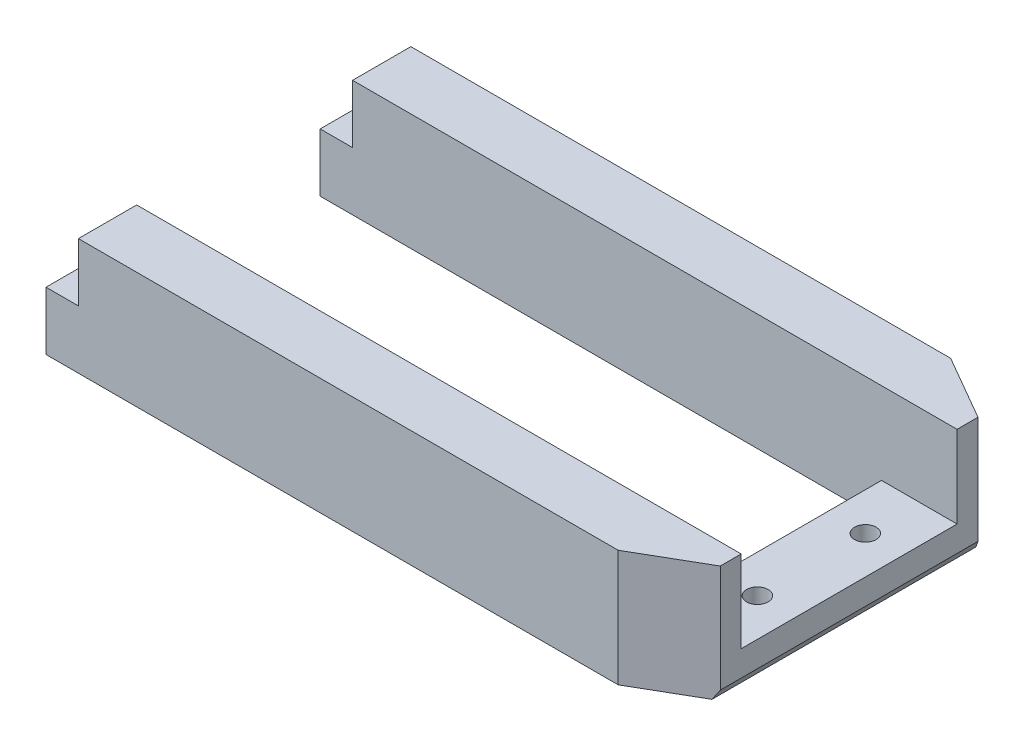
SolidWorks part; units mm, degrees
ref_plane "Alzado" through (0, 0, 0) normal (0, 0, 1) x (1, 0, 0)
ref_plane "Planta" through (0, 0, 0) normal (0, 1, 0) x (1, 0, 0)
ref_plane "Vista lateral" through (0, 0, 0) normal (1, 0, 0) x (0, 0, -1)
sketch "Croquis1" plane through (0, 0, 0) normal (0, 1, 0) x (1, 0, 0)
  line L0 (-29.0045, -14.5329) -> (-29.0045, -9.1329)
  line L1 (-29.0045, -9.1329) -> (22.9955, -9.1329)
  line L2 (22.9955, -9.1329) -> (22.9955, 10.8671)
  line L3 (22.9955, 10.8671) -> (-29.0045, 10.8671)
  line L4 (-29.0045, 10.8671) -> (-29.0045, 16.2671)
  line L5 (-29.0045, 16.2671) -> (23.9988, 16.2671)
  line L6 (23.9988, 16.2671) -> (29.9955, 12.8049)
  line L7 (29.9955, 12.8049) -> (29.9955, -11.0708)
  line L8 (29.9955, -11.0708) -> (23.9988, -14.5329)
  line L9 (23.9988, -14.5329) -> (-29.0045, -14.5329)
extrude "Saliente-Extruir1" add sketch "Croquis1" along normal blind 13
sketch "Croquis2" plane through (0, 13, 0) normal (0, 1, 0) x (1, 0, 0)
  line L0 (29.9955, -11.0708) -> (29.9955, 12.8049) construction
  line L1 (22.9955, 10.8671) -> (29.9955, 10.8671)
  line L2 (22.9955, 10.8671) -> (22.9955, -9.1329)
  line L3 (22.9955, -9.1329) -> (29.9955, -9.1329)
  line L4 (29.9955, 10.8671) -> (29.9955, -9.1329)
  dimension "D1" = 20
extrude "Cortar-Extruir1" cut sketch "Croquis2" against normal blind 7.6
sketch "Croquis3" plane through (0, 13, 0) normal (0, 1, 0) x (1, 0, 0)
  line L0 (-29.0045, 10.8671) -> (29.9955, 10.8671) construction
  line L1 (-29.0045, 16.2671) -> (-26.0045, 16.2671)
  line L2 (-29.0045, 16.2671) -> (-29.0045, 10.8671)
  line L3 (-29.0045, 10.8671) -> (-26.0045, 10.8671)
  line L4 (-26.0045, 16.2671) -> (-26.0045, 10.8671)
  line L5 (-29.0045, -14.5329) -> (23.9988, -14.5329) construction
  line L6 (-29.0045, -9.1329) -> (-26.0045, -9.1329)
  line L7 (-29.0045, -9.1329) -> (-29.0045, -14.5329)
  line L8 (-29.0045, -14.5329) -> (-26.0045, -14.5329)
  line L9 (-26.0045, -9.1329) -> (-26.0045, -14.5329)
  dimension "D1" = 3
extrude "Cortar-Extruir2" cut sketch "Croquis3" against normal blind 5.4
sketch "Croquis4" plane through (0, 5.4, 0) normal (0, 1, 0) x (1, 0, 0)
  line L0 (-26.0045, 10.8671) -> (29.9955, 10.8671) construction
  line L1 (29.9955, -9.1329) -> (29.9955, 10.8671) construction
  line L2 (29.9955, -9.1329) -> (-26.0045, -9.1329) construction
  circle A0 centre (26.4955, 5.8671) radius 1
  circle A1 centre (26.4955, -4.1329) radius 1
  dimension "D4" = 2
  dimension "D1" = 5
  dimension "D2" = 3.5
  dimension "D3" = 5
extrude "Cortar-Extruir3" cut sketch "Croquis4" against normal blind 10.4
sketch "Croquis5" plane through (0, 0, 14.5329) normal (0, 0, 1) x (1, 0, 0)
  line L0 (28.2355, 0) -> (29.9955, 3.04)
  line L1 (23.9988, 0) -> (29.9955, 0) construction
  line L2 (29.9955, 13) -> (29.9955, 0) construction
  line L3 (29.9955, 3.04) -> (29.9955, 0)
  line L4 (29.9955, 0) -> (28.2355, 0)
  dimension "D1" = 3.04
  dimension "D2" = 1.76
extrude "Cortar-Extruir4" cut sketch "Croquis5" against normal blind 32.4
sketch "Croquis6" plane through (0, 0, -16.2671) normal (0, 0, -1) x (-1, 0, 0)
  line L1 (29.0045, 0) -> (-37.6377, 0)
  line L2 (29.0045, 0) -> (29.0045, 2.2)
  line L3 (29.0045, 2.2) -> (-37.6377, 2.2)
  line L4 (-37.6377, 0) -> (-37.6377, 2.2)
  dimension "D1" = 2.2
extrude "Cortar-Extruir5" cut sketch "Croquis6" against normal blind 35
